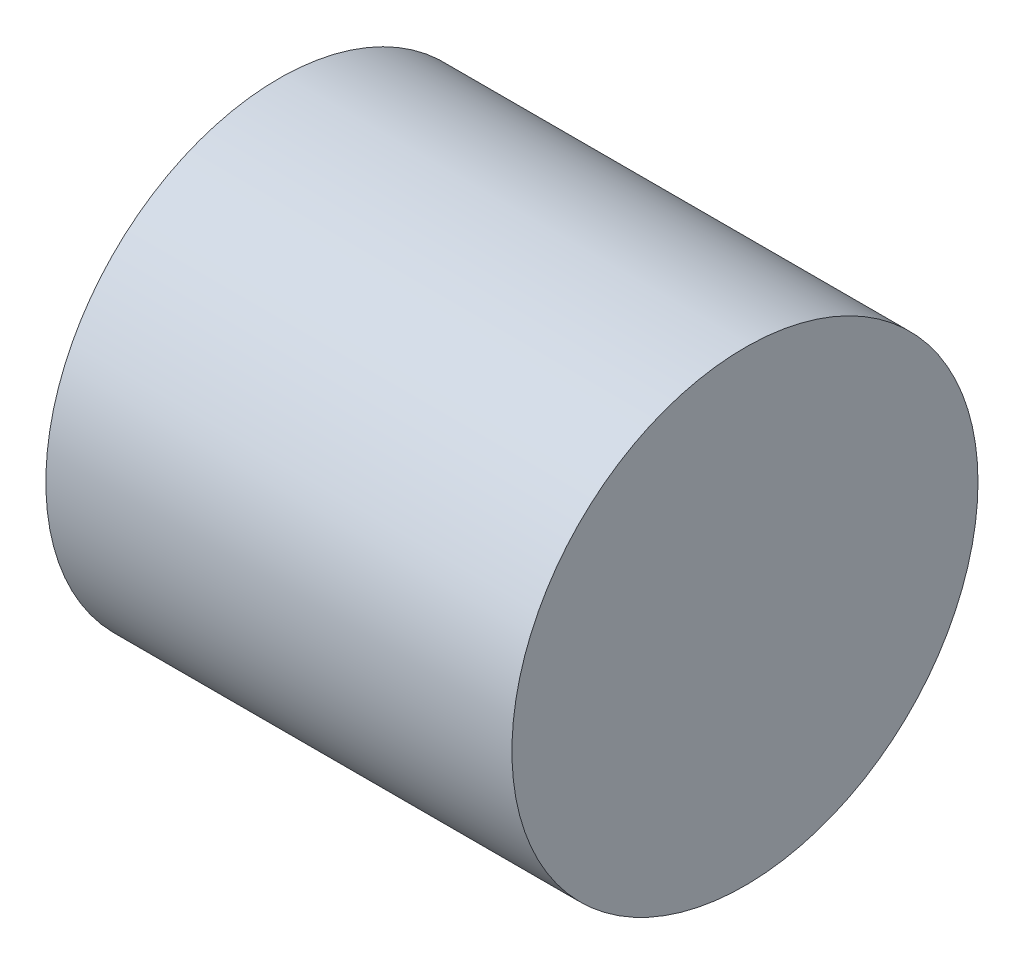
SolidWorks part; units mm, degrees
material "Titanium Ti-5Al-2.5Sn"
ref_plane "Front Plane" through (0, 0, 0) normal (0, 0, 1) x (1, 0, 0)
ref_plane "Top Plane" through (0, 0, 0) normal (0, 1, 0) x (1, 0, 0)
ref_plane "Right Plane" through (0, 0, 0) normal (1, 0, 0) x (0, 0, -1)
sketch "Sketch1" plane through (0, 0, 0) normal (1, 0, 0) x (0, 0, -1)
  circle A0 centre (0, 0) radius 1.5875
extrude "Boss-Extrude1" add sketch "Sketch1" along normal blind 3.175
